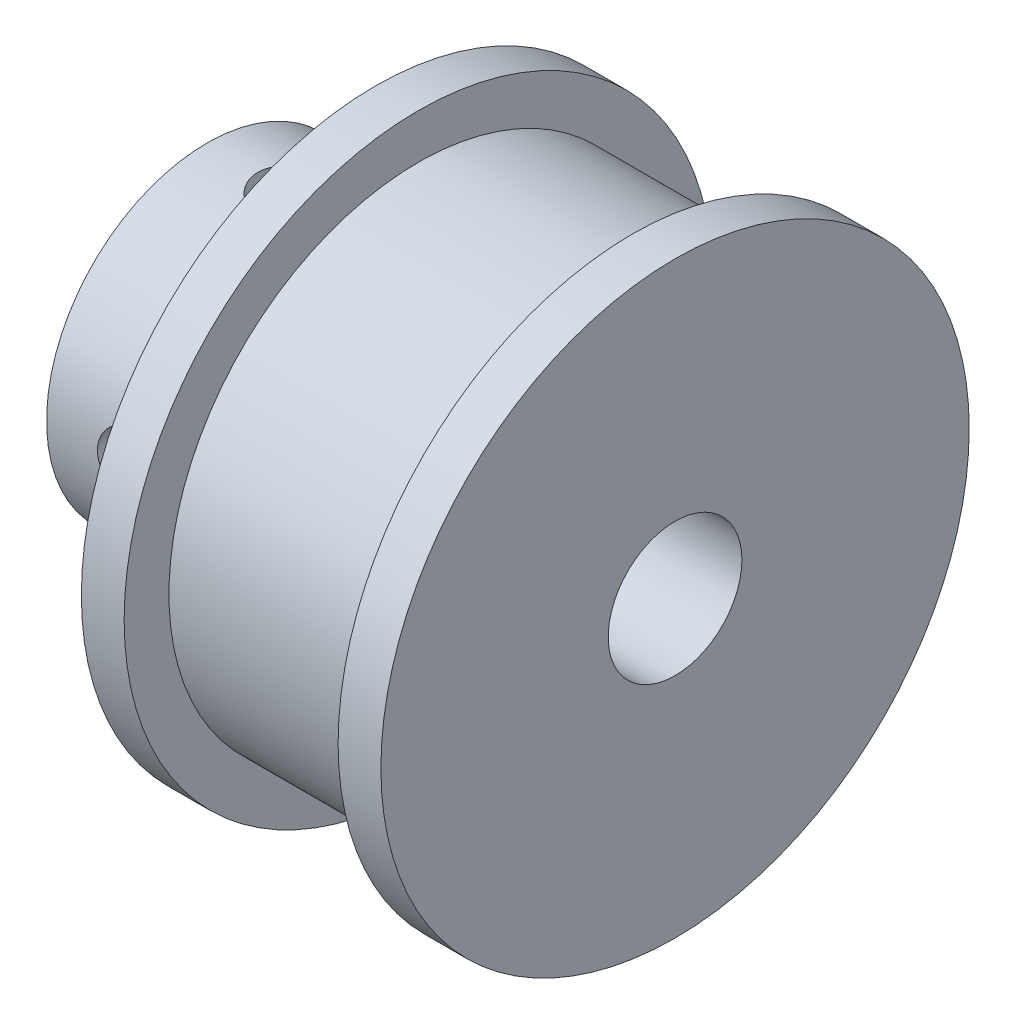
SolidWorks part; units mm, degrees
material "6061-T6 (SS)"
ref_plane "Front Plane" through (0, 0, 0) normal (0, 0, 1) x (1, 0, 0)
ref_plane "Top Plane" through (0, 0, 0) normal (0, 1, 0) x (1, 0, 0)
ref_plane "Right Plane" through (0, 0, 0) normal (1, 0, 0) x (0, 0, -1)
sketch "Sketch1" plane through (0, 0, 0) normal (0, 0, 1) x (1, 0, 0)
  line L0 (0, 2.5) -> (0, 6)
  line L1 (6.3, 11) -> (7.9, 11)
  line L2 (7.9, 11) -> (7.9, 9.325)
  line L3 (7.9, 9.325) -> (15.9, 9.325)
  line L4 (15.9, 9.325) -> (15.9, 11)
  line L5 (15.9, 11) -> (17.5, 11)
  line L6 (17.5, 11) -> (17.5, 2.5)
  line L7 (17.5, 2.5) -> (0, 2.5)
  line L8 (0, 0) -> (-7.6744, 0) construction
  line L9 (6.3, 11) -> (6.3, 6)
  line L10 (6.3, 6) -> (0, 6)
  dimension "D1" = 5
  dimension "D2" = 22
  dimension "D3" = 18.65
  dimension "D4" = 11.2
  dimension "D5" = 17.5
  dimension "D6" = 1.6
  dimension "D7" = 12
revolve "Revolve1" add sketch "Sketch1" angle 360 about L8
hole_wizard "M3x0.5 Tapped Hole1" positions "Sketch3" profile "Sketch2" tap size "M3x0.5" standard "ANSI Metric"
sketch "Sketch3" plane through (0, 0, 0) normal (0, 1, 0) x (1, 0, 0)
  line L0 (0, 0) -> (6.3, 0) construction
  line L2 (6.3, 6) -> (6.3, -6) construction
  point P8 (3.15, 0)
sketch "Sketch2" plane through (3.15, 0, 0) normal (1, 0, 0) x (0, 0, -1)
  line L0 (0, 0) -> (0, 11)
  line L1 (0, 11) -> (1.25, 11)
  line L2 (1.25, 11) -> (1.25, 0)
  line L5 (1.25, 0) -> (0, 0)
  line L11 (0, -6.35) -> (0, 107.95) construction
  dimension "Thread Major Dia." = 2.5
  dimension "Thru Tap Drill Depth" = 11
hole_wizard "M3x0.5 Tapped Hole2" positions "Sketch5" profile "Sketch4" tap size "M3x0.5" standard "ANSI Metric"
sketch "Sketch5" plane through (0, 0, 0) normal (0, 0, 1) x (1, 0, 0)
  line L0 (0, 0) -> (6.3, 0) construction
  line L2 (6.3, 11) -> (6.3, -11) construction
  point P7 (3.15, 0)
sketch "Sketch4" plane through (3.15, 0, 0) normal (1, 0, 0) x (0, 1, 0)
  line L0 (0, 0) -> (0, 11)
  line L1 (0, 11) -> (1.25, 11)
  line L2 (1.25, 11) -> (1.25, 0)
  line L5 (1.25, 0) -> (0, 0)
  line L11 (0, -6.35) -> (0, 107.95) construction
  dimension "Thread Major Dia." = 2.5
  dimension "Thru Tap Drill Depth" = 11
